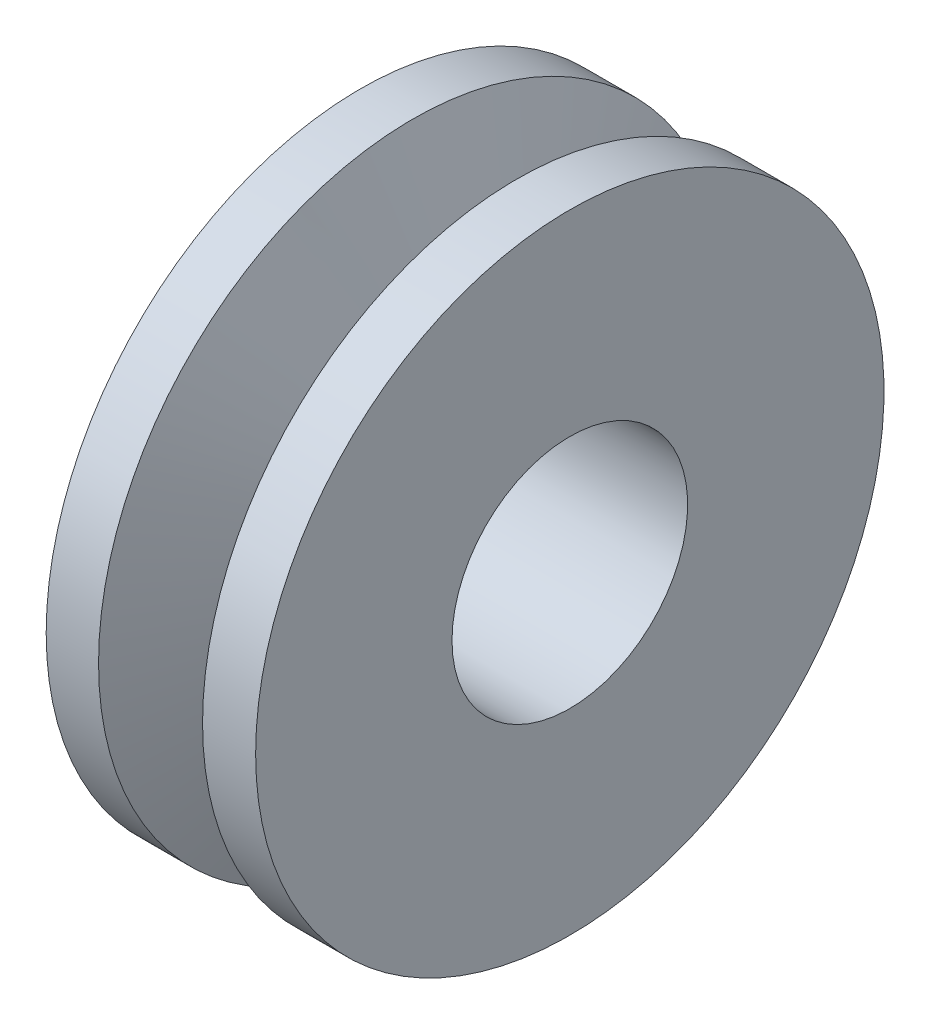
SolidWorks part; units mm, degrees
ref_plane "Front Plane" through (0, 0, 0) normal (0, 0, 1) x (1, 0, 0)
ref_plane "Top Plane" through (0, 0, 0) normal (0, 1, 0) x (1, 0, 0)
ref_plane "Right Plane" through (0, 0, 0) normal (1, 0, 0) x (0, 0, -1)
sketch "Sketch1" plane through (0, 0, 0) normal (0, 0, 1) x (1, 0, 0)
  line L0 (-5, 0) -> (5, 0) construction
  line L1 (-5, 5.625) -> (-5, 15)
  line L2 (-5, 15) -> (-2.5, 15)
  line L3 (5, 15) -> (5, 5.625)
  line L4 (5, 15) -> (2.4655, 15)
  line L5 (-5, 5.625) -> (5, 5.625)
  line L6 (-2.5, 15) -> (0, 9.0062)
  line L7 (2.4655, 15) -> (0, 9.0062)
  point P4 (0, 0)
  dimension "D1" = 10
  dimension "D2" = 2.5
  dimension "D3" = 45
  dimension "D4" = 15
  dimension "D5" = 5.625
  dimension "D6" = 10
revolve "Revolve1" add sketch "Sketch1" angle 360 about L0
